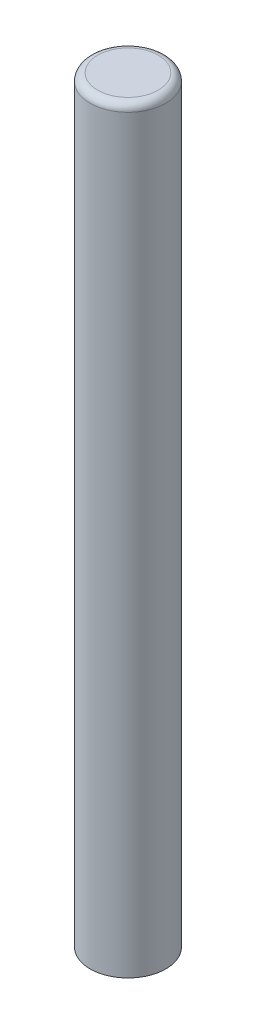
SolidWorks part; units mm, degrees
material "AISI 1020"
ref_plane "Front Plane" through (0, 0, 0) normal (0, 0, 1) x (1, 0, 0)
ref_plane "Top Plane" through (0, 0, 0) normal (0, 1, 0) x (1, 0, 0)
ref_plane "Right Plane" through (0, 0, 0) normal (1, 0, 0) x (0, 0, -1)
sketch "Sketch1" plane through (0, 0, 0) normal (0, 1, 0) x (1, 0, 0)
  circle A0 centre (0, 0) radius 5
extrude "Boss-Extrude1" add sketch "Sketch1" along normal blind 100
fillet "Fillet1" radius 1 1 edges at (0, 100, 5)
